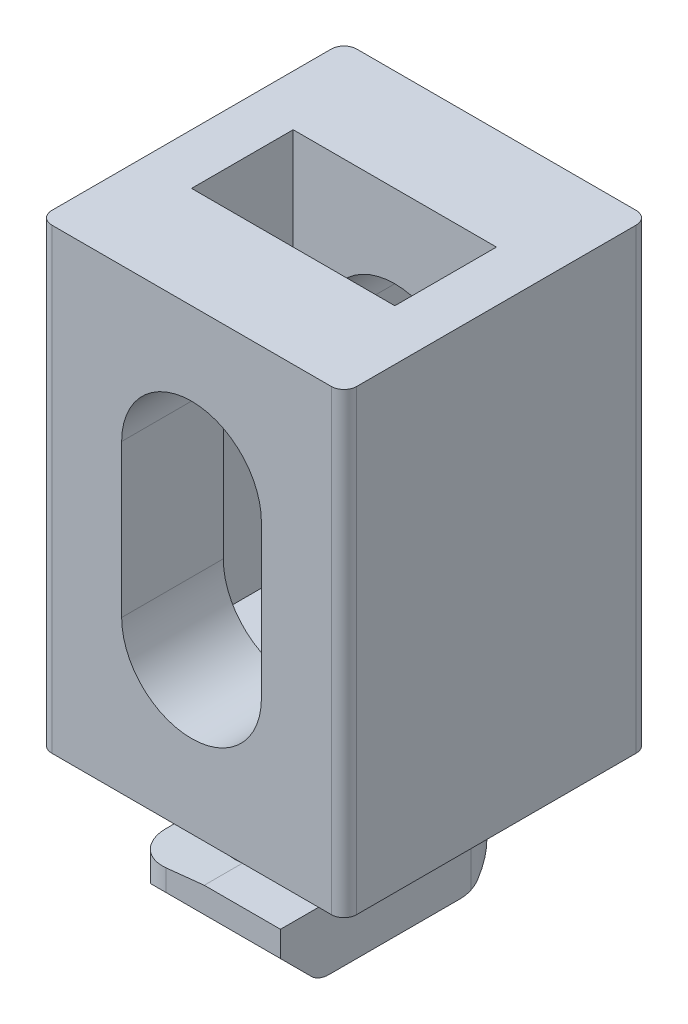
SolidWorks part; units mm, degrees
ref_plane "前视基准面" through (0, 0, 0) normal (0, 0, 1) x (1, 0, 0)
ref_plane "上视基准面" through (0, 0, 0) normal (0, 1, 0) x (1, 0, 0)
ref_plane "右视基准面" through (0, 0, 0) normal (1, 0, 0) x (0, 0, -1)
sketch "草图1" plane through (0, 0, 0) normal (0, 0, 1) x (1, 0, 0)
  line L1 (0, 0) -> (12, 0)
  line L2 (0, 0) -> (0, 18)
  line L3 (0, 18) -> (12, 18)
  line L4 (12, 0) -> (12, 18)
  dimension "D1" = 12
  dimension "D2" = 18
extrude "拉伸1" add sketch "草图1" along normal blind 12
sketch "草图2" plane through (0, 0, 12) normal (0, 0, 1) x (1, 0, 0)
  line L0 (3.25, 12) -> (3.25, 6)
  line L1 (8.75, 12) -> (8.75, 6)
  line L2 (0, 18) -> (0, 0) construction
  line L3 (12, 18) -> (0, 18) construction
  arc A0 (3.25, 12) -> (8.75, 12) centre (6, 12) cw
  arc A1 (3.25, 6) -> (8.75, 6) centre (6, 6) ccw
  dimension "D3" = 2.75
  dimension "D4" = 2.75
  dimension "D6" = 6
  dimension "D1" = 5.5
  dimension "D2" = 3.25
  dimension "D5" = 6
extrude "切除-拉伸1" cut sketch "草图2" against normal blind 12
sketch "草图3" plane through (0, 18, 0) normal (0, 1, 0) x (1, 0, 0)
  line L0 (0, -12) -> (0, 0) construction
  line L1 (2, -4) -> (10, -4)
  line L2 (2, -4) -> (2, -8)
  line L3 (2, -8) -> (10, -8)
  line L4 (10, -4) -> (10, -8)
  line L5 (12, -12) -> (0, -12) construction
  dimension "D1" = 8
  dimension "D2" = 4
  dimension "D3" = 2
  dimension "D4" = 4
extrude "切除-拉伸2" cut sketch "草图3" against normal blind 15
sketch "草图4" plane through (0, 0, 0) normal (0, -1, 0) x (1, 0, 0)
  line L0 (9, 10) -> (6, 10)
  line L1 (0, 12) -> (0, 0) construction
  line L2 (0, 12) -> (12, 12) construction
  line L5 (9, 10) -> (9, 7)
  line L6 (3, 4) -> (6, 4)
  line L7 (3, 4) -> (3, 7)
  arc A0 (6, 10) -> (3, 7) centre (6, 7) ccw
  arc A1 (6, 4) -> (9, 7) centre (6, 7) ccw
  dimension "D1" = 3
  dimension "D2" = 3
  dimension "D3" = 3
  dimension "D4" = 3
  dimension "D5" = 3
  dimension "D6" = 2
extrude "拉伸2" add sketch "草图4" along normal blind 4.5
sketch "草图5" plane through (0, -4.5, 0) normal (0, -1, 0) x (1, 0, 0)
  line L1 (3, 11.5) -> (9, 11.5)
  line L2 (3, 11.5) -> (3, 2.5)
  line L3 (3, 2.5) -> (9, 2.5)
  line L4 (9, 11.5) -> (9, 2.5)
  line L6 (0, 0) -> (12, 0) construction
  line L8 (12, 12) -> (12, 0) construction
  dimension "D1" = 9
  dimension "D2" = 6
  dimension "D3" = 3
  dimension "D4" = 2.5
extrude "拉伸3" add sketch "草图5" against normal blind 2.5
fillet "圆角2" radius 0.5 4 edges at (12, 9, 12) (0, 9, 0) (12, 9, 0) (0, 9, 12)
chamfer "倒角3" distance 1.5 angle 45 1 edges at (6, -4.5, 11.5)
chamfer "倒角4" distance 1.5 angle 45 1 edges at (6, -4.5, 2.5)
fillet "圆角3" radius 1 2 edges at (6, -4.5, 4) (6, -4.5, 10)
sketch "草图8" plane through (0, 0, 11.5) normal (0, 0, 1) x (1, 0, 0)
  line L0 (6, -2) -> (3, -2)
  line L1 (9, -2) -> (3, -2) construction
  line L2 (3, -2) -> (3, -2.3153)
  line L4 (3, -2) -> (3, -3) construction
  line L5 (3, -2.3153) -> (6, -2)
  dimension "D1" = 6
extrude "切除-拉伸3" cut sketch "草图8" against normal up to surface (4.5 mm away)
sketch "草图9" plane through (0, 0, 2.5) normal (0, 0, -1) x (-1, 0, 0)
  line L0 (-6, -2) -> (-9, -2)
  line L1 (-9, -2) -> (-9, -2.3153)
  line L2 (-9, -2) -> (-9, -3) construction
  line L3 (-9, -2.3153) -> (-6, -2)
  dimension "D1" = 6
extrude "切除-拉伸4" cut sketch "草图9" against normal up to surface (4.5 mm away)
fillet "圆角6" radius 1.5 1 edges at (9, -2.6577, 2.5)
fillet "圆角7" radius 1.5 1 edges at (3, -2.6577, 11.5)
